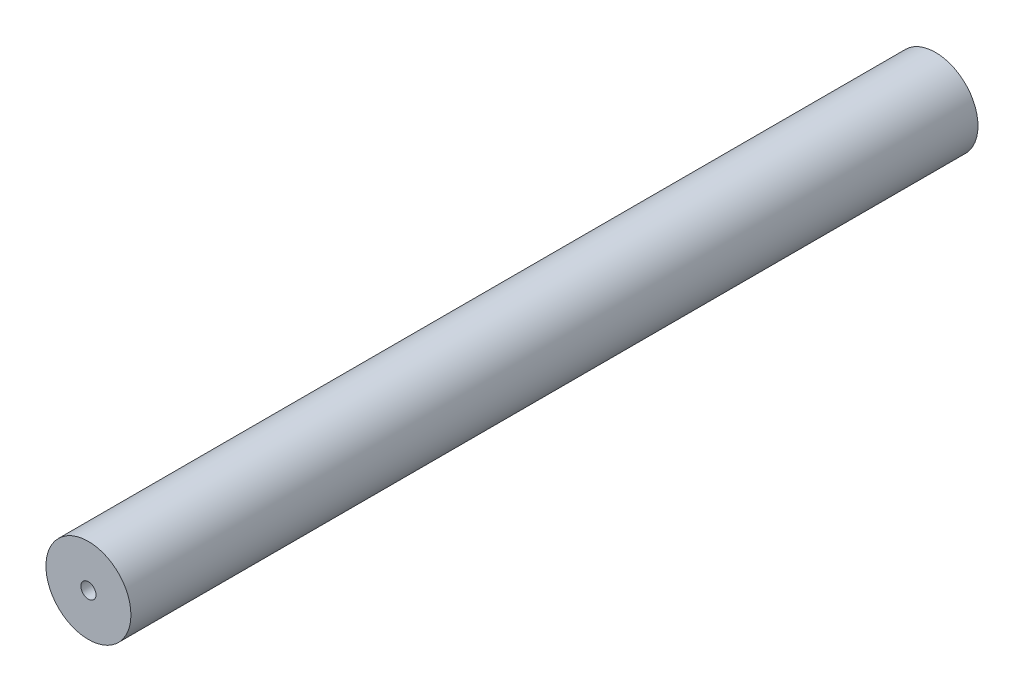
SolidWorks part; units mm, degrees
material "ABS PC"
ref_plane "Front Plane" through (0, 0, 0) normal (0, 0, 1) x (1, 0, 0)
ref_plane "Top Plane" through (0, 0, 0) normal (0, 1, 0) x (1, 0, 0)
ref_plane "Right Plane" through (0, 0, 0) normal (1, 0, 0) x (0, 0, -1)
sketch "Sketch1" plane through (0, 0, 0) normal (0, 0, 1) x (1, 0, 0)
  circle A0 centre (0, 0) radius 2.25
  circle A1 centre (0, 0) radius 0.4
  dimension "D1" = 4.5
  dimension "D2" = 0.8
extrude "Boss-Extrude1" add sketch "Sketch1" along normal blind 44.85
